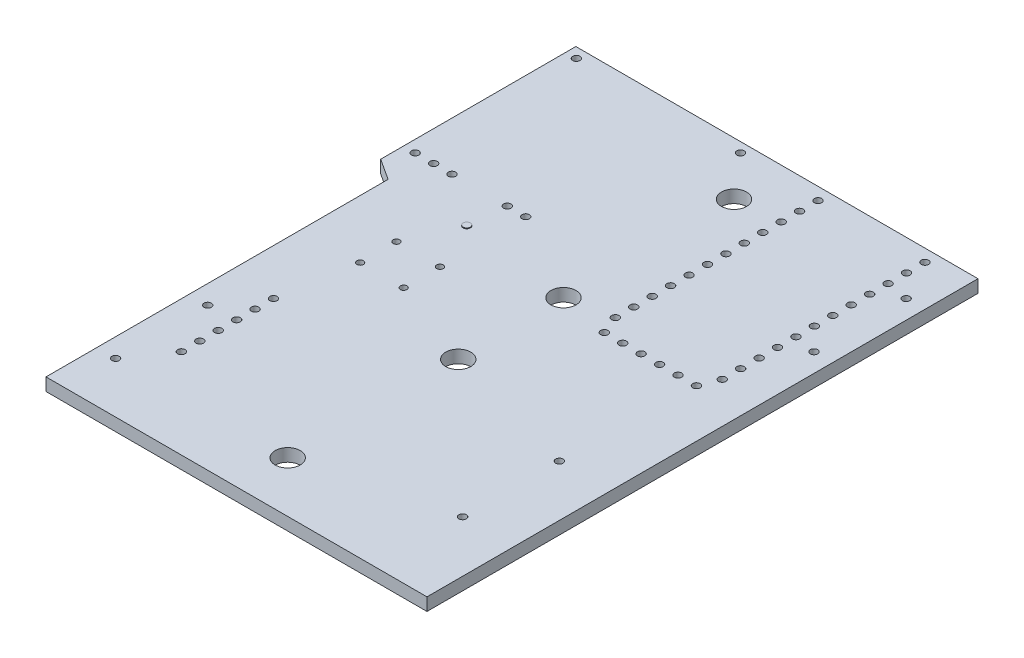
SolidWorks part; units mm, degrees
ref_plane "Front Plane" through (0, 0, 0) normal (0, 0, 1) x (1, 0, 0)
ref_plane "Top Plane" through (0, 0, 0) normal (0, 1, 0) x (1, 0, 0)
ref_plane "Right Plane" through (0, 0, 0) normal (1, 0, 0) x (0, 0, -1)
sketch "Sketch1" plane through (0, 0, 0) normal (0, 1, 0) x (1, 0, 0)
  line L0 (0, 0) -> (0, 37.975) construction
  line L1 (0, 0) -> (27.715, 0) construction
  line L2 (-27.715, 37.975) -> (27.715, 37.975)
  line L3 (27.715, 37.975) -> (27.715, -37.975)
  line L4 (27.715, -37.975) -> (-24.795, -37.975)
  line L6 (-24.795, -37.975) -> (-24.795, 9.175)
  line L7 (-24.795, 9.175) -> (-27.715, 11.075)
  line L8 (-27.715, 11.075) -> (-27.715, 37.975)
  dimension "D1" = 52.51
  dimension "D2" = 55.43
  dimension "D3" = 75.95
  dimension "D4" = 47.15
  dimension "D5" = 26.9
extrude "Boss-Extrude1" add sketch "Sketch1" along normal mid plane 1.75
sketch "Sketch2" plane through (0, 0.875, 0) normal (0, 1, 0) x (1, 0, 0)
  line L0 (1.5194, -30.9773) -> (-24.795, -30.9773) construction
  line L1 (1.4133, 30.6471) -> (27.715, 30.6471) construction
  line L6 (27.715, -37.975) -> (27.715, 37.975)
  line L7 (27.715, 37.975) -> (-27.715, 37.975)
  line L8 (-27.715, 37.975) -> (-27.715, 11.075)
  line L9 (-27.715, 11.075) -> (-24.795, 9.175)
  line L10 (-24.795, 9.175) -> (-24.795, -37.975)
  line L11 (-24.795, -37.975) -> (27.715, -37.975)
  line L12 (27.715, -37.975) -> (27.715, 37.975)
  line L13 (27.715, 37.975) -> (-27.715, 37.975)
  line L14 (-27.715, 37.975) -> (-27.715, 11.075)
  line L15 (-27.715, 11.075) -> (-24.795, 9.175)
  line L16 (-24.795, 9.175) -> (-24.795, -37.975)
  line L17 (-24.795, -37.975) -> (27.715, -37.975)
  circle A0 centre (1.4133, 30.6471) radius 1.7272
  circle A1 centre (1.4133, 7.1394) radius 1.7272
  circle A2 centre (1.5194, -7.4696) radius 1.7272
  circle A3 centre (1.5194, -30.9773) radius 1.7272
  circle A4 centre (-22.2042, -30.9773) radius 0.508
  circle A5 centre (-22.2042, -18.2773) radius 0.508
  circle A6 centre (25.1369, 30.6471) radius 0.508
  circle A7 centre (25.1369, 17.9471) radius 0.508
  dimension "D2" = 3.4544
  dimension "D9" = 1.016
  dimension "D14" = 1.016
  dimension "D3" = 23.5077
  dimension "D4" = 23.5077
  dimension "D5" = 5.2705
  dimension "D6" = 5.6007
  dimension "D7" = 2.5908
  dimension "D8" = 12.7
  dimension "D10" = 23.7236
  dimension "D11" = 12.7
  dimension "D12" = 23.7236
  dimension "D13" = 2.5781
  dimension "D1" = 0
extrude "Cut-Extrude1" cut sketch "Sketch2" against normal through all
sketch "Sketch4" plane through (0, 0.875, 0) normal (0, 1, 0) x (1, 0, 0)
  line L0 (-18.4704, 37.975) -> (-18.4704, -37.975) construction
  line L6 (27.715, -37.975) -> (27.715, 37.975)
  line L7 (27.715, 37.975) -> (-27.715, 37.975)
  line L8 (-27.715, 37.975) -> (-27.715, 11.075)
  line L9 (-27.715, 11.075) -> (-24.795, 9.175)
  line L10 (-24.795, 9.175) -> (-24.795, -37.975)
  line L11 (-24.795, -37.975) -> (27.715, -37.975)
  line L12 (27.715, -37.975) -> (27.715, 37.975)
  line L13 (27.715, 37.975) -> (-27.715, 37.975)
  line L14 (-27.715, 37.975) -> (-27.715, 11.075)
  line L15 (-27.715, 11.075) -> (-24.795, 9.175)
  line L16 (-24.795, 9.175) -> (-24.795, -37.975)
  line L17 (-24.795, -37.975) -> (27.715, -37.975)
  circle A0 centre (-18.4704, -12.9433) radius 0.508
  circle A1 centre (-18.4704, -15.4833) radius 0.508
  circle A2 centre (-18.4704, -18.0233) radius 0.508
  circle A3 centre (-18.4704, -20.5633) radius 0.508
  circle A4 centre (-18.4704, -23.1033) radius 0.508
  circle A5 centre (-18.4704, -25.6433) radius 0.508
  dimension "D8" = 1.016
  dimension "D2" = 6.3246
  dimension "D3" = 2.54
  dimension "D4" = 2.54
  dimension "D5" = 2.54
  dimension "D6" = 2.54
  dimension "D7" = 2.54
  dimension "D9" = 25.0317
  dimension "D1" = 0
extrude "Cut-Extrude2" cut sketch "Sketch4" against normal through all contours L0 A0 | A0 L0 | L0 A1 | A1 L0 | A2 L0 | L0 A2 | L0 A3 | A3 L0 | L0 A4 | A4 L0 | A5 L0 | L0 A5
sketch "Sketch5" plane through (0, 0.875, 0) normal (0, 1, 0) x (1, 0, 0)
  line L6 (27.715, -37.975) -> (27.715, 37.975)
  line L7 (27.715, 37.975) -> (-27.715, 37.975)
  line L8 (-27.715, 37.975) -> (-27.715, 11.075)
  line L9 (-27.715, 11.075) -> (-24.795, 9.175)
  line L10 (-24.795, 9.175) -> (-24.795, -37.975)
  line L11 (-24.795, -37.975) -> (27.715, -37.975)
  line L12 (27.715, -37.975) -> (27.715, 37.975)
  line L13 (27.715, 37.975) -> (-27.715, 37.975)
  line L14 (-27.715, 37.975) -> (-27.715, 11.075)
  line L15 (-27.715, 11.075) -> (-24.795, 9.175)
  line L16 (-24.795, 9.175) -> (-24.795, -37.975)
  line L17 (-24.795, -37.975) -> (27.715, -37.975)
  circle A0 centre (-26.0894, 14.2006) radius 0.508
  circle A1 centre (-23.5494, 14.2006) radius 0.508
  circle A2 centre (-21.0094, 14.2006) radius 0.508
  circle A3 centre (-13.3894, 14.2006) radius 0.508
  circle A4 centre (-10.8494, 14.2006) radius 0.508
  dimension "D7" = 1.016
  dimension "D2" = 1.6256
  dimension "D3" = 2.54
  dimension "D4" = 2.54
  dimension "D5" = 7.62
  dimension "D6" = 2.54
  dimension "D8" = 23.7744
  dimension "D1" = 0
extrude "Cut-Extrude3" cut sketch "Sketch5" against normal through all contours A0 | A1 | A2 | A3 | A4
sketch "Sketch6" plane through (0, 0.875, 0) normal (0, 1, 0) x (1, 0, 0)
  line L0 (14.7356, 37.975) -> (14.7356, 0) construction
  line L6 (27.715, -37.975) -> (27.715, 37.975)
  line L7 (27.715, 37.975) -> (-27.715, 37.975)
  line L8 (-27.715, 37.975) -> (-27.715, 11.075)
  line L9 (-27.715, 11.075) -> (-24.795, 9.175)
  line L10 (-24.795, 9.175) -> (-24.795, -37.975)
  line L11 (-24.795, -37.975) -> (27.715, -37.975)
  line L12 (27.715, -37.975) -> (27.715, 37.975)
  line L13 (27.715, 37.975) -> (-27.715, 37.975)
  line L14 (-27.715, 37.975) -> (-27.715, 11.075)
  line L15 (-27.715, 11.075) -> (-24.795, 9.175)
  line L16 (-24.795, 9.175) -> (-24.795, -37.975)
  line L17 (-24.795, -37.975) -> (27.715, -37.975)
  circle A0 centre (22.1016, 36.2732) radius 0.508
  circle A1 centre (22.1016, 33.7332) radius 0.508
  circle A2 centre (22.1016, 31.1932) radius 0.508
  circle A3 centre (22.1016, 28.6532) radius 0.508
  circle A4 centre (22.1016, 26.1132) radius 0.508
  circle A5 centre (22.1016, 23.5732) radius 0.508
  circle A6 centre (22.1016, 21.0332) radius 0.508
  circle A7 centre (22.1016, 18.4932) radius 0.508
  circle A8 centre (22.1016, 15.9532) radius 0.508
  circle A9 centre (22.1016, 13.4132) radius 0.508
  circle A10 centre (22.1016, 10.8732) radius 0.508
  circle A11 centre (22.1016, 8.3332) radius 0.508
  circle A12 centre (21.0856, 5.7932) radius 0.508
  circle A13 centre (18.5456, 5.7932) radius 0.508
  circle A14 centre (16.0056, 5.7932) radius 0.508
  circle A15 centre (13.4656, 5.7932) radius 0.508
  circle A16 centre (10.9256, 5.7932) radius 0.508
  circle A17 centre (8.3856, 5.7932) radius 0.508
  circle A18 centre (7.3696, 8.3332) radius 0.508
  circle A19 centre (7.3696, 10.8732) radius 0.508
  circle A20 centre (7.3696, 13.4132) radius 0.508
  circle A21 centre (7.3696, 15.9532) radius 0.508
  circle A22 centre (7.3696, 18.4932) radius 0.508
  circle A23 centre (7.3696, 21.0332) radius 0.508
  circle A24 centre (7.3696, 23.5732) radius 0.508
  circle A25 centre (7.3696, 26.1132) radius 0.508
  circle A26 centre (7.3696, 28.6532) radius 0.508
  circle A27 centre (7.3696, 31.1932) radius 0.508
  circle A28 centre (7.3696, 33.7332) radius 0.508
  circle A29 centre (7.3696, 36.2732) radius 0.508
  dimension "D2" = 1.016
  dimension "D3" = 1.7018
  dimension "D4" = 5.6134
  dimension "D5" = 14.732
  dimension "D6" = 2.54
  dimension "D7" = 2.54
  dimension "D8" = 2.54
  dimension "D9" = 2.54
  dimension "D10" = 2.54
  dimension "D11" = 2.54
  dimension "D12" = 2.54
  dimension "D13" = 2.54
  dimension "D14" = 2.54
  dimension "D15" = 2.54
  dimension "D16" = 2.54
  dimension "D17" = 2.54
  dimension "D18" = 2.54
  dimension "D19" = 2.54
  dimension "D20" = 30.48
  dimension "D1" = 0
extrude "Cut-Extrude4" cut sketch "Sketch6" against normal through all contours A29 | A28 | A27 | A26 | A25 | A24 | A23 | A22 | A21 | A20 | A19 | A18 | A17 | A16 | A15 | A14 | A13 | A12 | A11 | A10 | A9 | A8 | A7 | A6 | A5 | A4 | A3 | A2 | A1 | A0
sketch "Sketch7" plane through (0, 0.875, 0) normal (0, 1, 0) x (1, 0, 0)
  line L6 (27.715, -37.975) -> (27.715, 37.975)
  line L7 (27.715, 37.975) -> (-27.715, 37.975)
  line L8 (-27.715, 37.975) -> (-27.715, 11.075)
  line L9 (-27.715, 11.075) -> (-24.795, 9.175)
  line L10 (-24.795, 9.175) -> (-24.795, -37.975)
  line L11 (-24.795, -37.975) -> (27.715, -37.975)
  line L12 (27.715, -37.975) -> (27.715, 37.975)
  line L13 (27.715, 37.975) -> (-27.715, 37.975)
  line L14 (-27.715, 37.975) -> (-27.715, 11.075)
  line L15 (-27.715, 11.075) -> (-24.795, 9.175)
  line L16 (-24.795, 9.175) -> (-24.795, -37.975)
  line L17 (-24.795, -37.975) -> (27.715, -37.975)
  circle A0 centre (-26.2545, 36.5907) radius 0.508
  circle A1 centre (-3.6612, 36.6161) radius 0.508
  circle A2 centre (20.6157, -25.9608) radius 0.508
  circle A3 centre (20.6411, -12.6512) radius 0.508
  dimension "D4" = 1.016
  dimension "D9" = 1.016
  dimension "D2" = 1.4605
  dimension "D3" = 1.3843
  dimension "D5" = 24.0538
  dimension "D6" = 1.3589
  dimension "D7" = 7.0993
  dimension "D8" = 12.0142
  dimension "D10" = 25.3238
  dimension "D11" = 7.0739
  dimension "D1" = 0
extrude "Cut-Extrude5" cut sketch "Sketch7" against normal through all contours A2 | A3 | A1 | A0
ref_plane "Plane1" through (1.46, 0, 0) normal (-1, 0, 0) x (0, 0, 1)
ref_plane "Plane2" through (0, 0, 0) normal (0, 0, -1) x (-1, 0, 0)
sketch "Sketch8" plane through (0, 0.875, 0) normal (0, 1, 0) x (1, 0, 0)
  line L0 (27.715, -37.975) -> (27.715, 37.975) construction
  line L1 (-24.795, -37.975) -> (27.715, -37.975) construction
  circle A0 centre (-16.7858, 2.3183) radius 0.45
  circle A1 centre (-10.7858, 2.3183) radius 0.45
  circle A2 centre (-16.7858, -2.6817) radius 0.45
  circle A3 centre (-10.7858, -2.6817) radius 0.45
  dimension "D9" = 0.9
  dimension "D1" = 44.5008
  dimension "D2" = 35.2933
  dimension "D3" = 6
  dimension "D4" = 5
extrude "Cut-Extrude6" cut sketch "Sketch8" against normal through all
sketch "Sketch9" plane through (0, 0.875, 0) normal (0, 1, 0) x (1, 0, 0)
  line L0 (-24.795, -37.975) -> (27.715, -37.975) construction
  line L1 (27.715, -37.975) -> (27.715, 37.975) construction
  circle A0 centre (-13.8267, 9.048) radius 0.5
  dimension "D3" = 1
  dimension "D1" = 47.023
  dimension "D2" = 41.5417
extrude "Boss-Extrude2" add sketch "Sketch9" along normal blind 0.1
ref_plane "Plane3" through (0, -1.3751, 0) normal (0, -1, 0) x (1, 0, 0)
sketch "Sketch10" plane through (0, 0.875, 0) normal (0, 1, 0) x (1, 0, 0)
  line L0 (-16.7858, 2.3183) -> (-10.7858, 2.3183) construction
  line L1 (-16.7858, -2.6817) -> (-10.7858, -2.6817) construction
  line L2 (-16.7858, 2.3183) -> (-10.7858, -2.6817) construction
  line L3 (-10.7858, -2.6817) -> (-10.7858, 2.3183) construction
  line L4 (-10.7858, 2.3183) -> (-16.7858, -2.6817) construction
  line L5 (-16.7858, -2.6817) -> (-16.7858, 2.3183) construction
  line L6 (-13.8267, 9.048) -> (-13.7858, -0.1817) construction
  line L7 (-13.7858, -0.1817) -> (-13.7858, -37.975) construction
  line L8 (-24.795, -37.975) -> (27.715, -37.975) construction
  circle A0 centre (-13.8267, 9.048) radius 0.5 construction
  circle A1 centre (-13.8267, 9.048) radius 0.5
  dimension "D1" = 9.2297
  dimension "D2" = 37.7933
